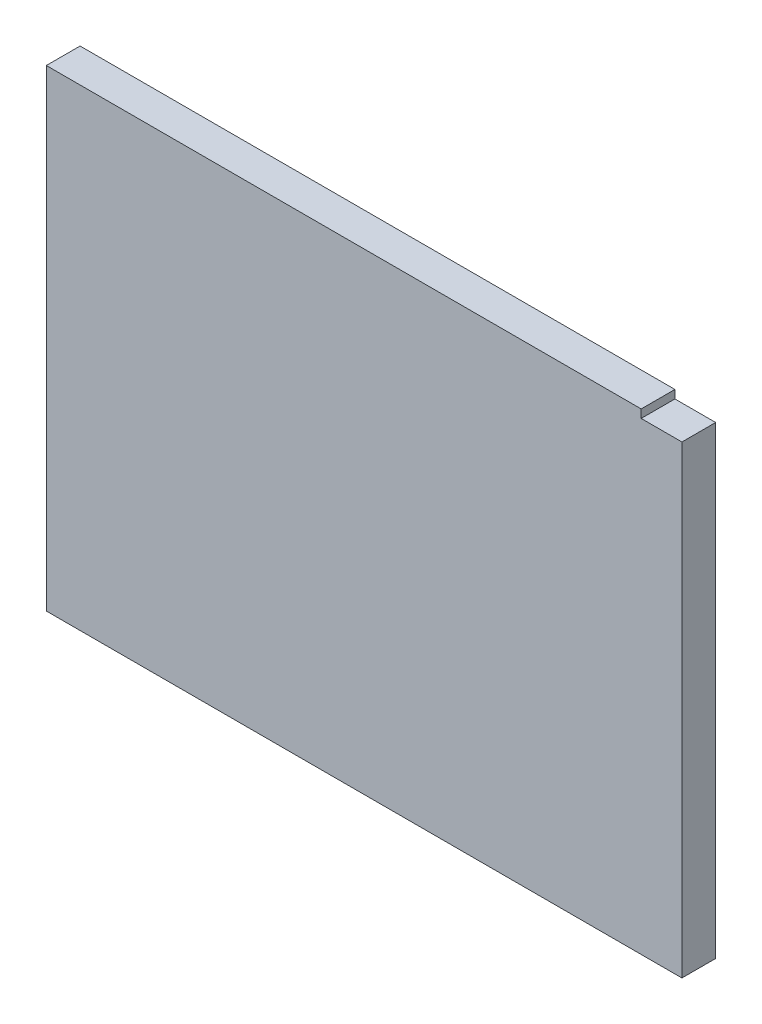
SolidWorks part; units mm, degrees
material "Pine"
ref_plane "Front Plane" through (0, 0, 0) normal (0, 0, 1) x (1, 0, 0)
ref_plane "Top Plane" through (0, 0, 0) normal (0, 1, 0) x (1, 0, 0)
ref_plane "Right Plane" through (0, 0, 0) normal (1, 0, 0) x (0, 0, -1)
sketch "Sketch1" plane through (0, 0, 0) normal (0, 0, 1) x (1, 0, 0)
  line L0 (-5300.6625, 1520.825) -> (-5451.475, 1520.825)
  line L1 (-5456.2375, 1384.3) -> (-5456.2375, 1516.0625)
  line L2 (-5557.8375, 1546.225) -> (-5194.3, 1546.225)
  line L3 (-5557.8375, 1539.875) -> (-5194.3, 1539.875)
  line L4 (-5297.4875, 1377.95) -> (-5454.65, 1377.95)
  line L5 (-5291.1375, 1384.3) -> (-5291.1375, 1516.0625)
  line L6 (-5300.6625, 1525.5875) -> (-5451.475, 1525.5875)
  line L7 (-5461, 1384.3) -> (-5461, 1516.0625)
  line L8 (-5297.4875, 1382.7125) -> (-5454.65, 1382.7125)
  line L9 (-5295.9, 1384.3) -> (-5295.9, 1516.0625)
  line L10 (-5740.4, 998.5375) -> (-5740.4, 1181.1)
  line L11 (-5740.4, 1181.1) -> (-5512.5938, 1181.1)
  line L12 (-5512.5938, 1181.1) -> (-5512.5938, 998.5375)
  line L13 (-5512.5938, 998.5375) -> (-5740.4, 998.5375)
  line L14 (-5258.5938, 1181.1) -> (-5486.4, 1181.1)
  line L15 (-5258.5938, 998.5375) -> (-5258.5938, 1181.1)
  line L16 (-5486.4, 998.5375) -> (-5258.5938, 998.5375)
  line L17 (-5486.4, 1181.1) -> (-5486.4, 998.5375)
  line L18 (-5740.4, 898.525) -> (-5011.7375, 898.525)
  line L19 (-5168.1062, 1384.3) -> (-5168.1062, 1392.2375)
  line L20 (-5176.0437, 1400.175) -> (-5245.8937, 1400.175)
  line L21 (-5253.8313, 1392.2375) -> (-5253.8313, 1384.3)
  line L22 (-5451.475, 1512.8875) -> (-5451.475, 1384.3)
  line L23 (-5303.8375, 1516.0625) -> (-5448.3, 1516.0625)
  line L24 (-5498.3062, 1384.3) -> (-5451.475, 1384.3)
  line L25 (-5253.8313, 1384.3) -> (-5300.6625, 1384.3)
  line L26 (-5584.0312, 1384.3) -> (-5740.4, 1384.3)
  line L27 (-5564.1875, 1536.7) -> (-5740.4, 1536.7)
  line L28 (-5740.4, 1357.3125) -> (-5740.4, 1206.5)
  line L29 (-5011.7375, 1357.3125) -> (-5740.4, 1357.3125)
  line L30 (-5011.7375, 1206.5) -> (-5011.7375, 1357.3125)
  line L31 (-5740.4, 1206.5) -> (-5011.7375, 1206.5)
  line L32 (-4765.675, 1549.4) -> (-4978.4, 1549.4)
  line L33 (-4765.675, 1397) -> (-4765.675, 1549.4)
  line L34 (-4978.4, 1397) -> (-4765.675, 1397)
  line L35 (-4978.4, 1549.4) -> (-4978.4, 1397)
  line L36 (-4765.675, 1371.6) -> (-4978.4, 1371.6)
  line L37 (-4765.675, 1219.2) -> (-4765.675, 1371.6)
  line L38 (-4978.4, 1219.2) -> (-4765.675, 1219.2)
  line L39 (-4978.4, 1371.6) -> (-4978.4, 1219.2)
  line L40 (-5284.7875, 803.275) -> (-5272.0875, 803.275)
  line L41 (-5187.95, 1536.7) -> (-5011.7375, 1536.7)
  line L42 (-5300.6625, 1384.3) -> (-5300.6625, 1512.8875)
  line L43 (-5740.4, 1536.7) -> (-5740.4, 1384.3)
  line L44 (-5557.8375, 1536.7) -> (-5557.8375, 1549.4)
  line L45 (-5557.8375, 1549.4) -> (-5194.3, 1549.4)
  line L46 (-5194.3, 1549.4) -> (-5194.3, 1536.7)
  line L47 (-5011.7375, 1536.7) -> (-5011.7375, 1384.3)
  line L48 (-5011.7375, 1384.3) -> (-5168.1062, 1384.3)
  line L49 (-5498.3062, 1384.3) -> (-5498.3062, 1392.2375)
  line L50 (-5506.2437, 1400.175) -> (-5576.0938, 1400.175)
  line L51 (-5584.0312, 1392.2375) -> (-5584.0312, 1384.3)
  line L52 (-5740.4, 660.4) -> (-5740.4, 898.525)
  line L53 (-5011.7375, 898.525) -> (-5011.7375, 660.4)
  line L54 (-5011.7375, 660.4) -> (-5740.4, 660.4)
  line L55 (-5291.1375, 803.275) -> (-5291.1375, 752.475)
  line L56 (-5265.7375, 752.475) -> (-5265.7375, 803.275)
  line L57 (-5284.7875, 752.475) -> (-5272.0875, 752.475)
  arc A0 (-5451.475, 1520.825) -> (-5456.2375, 1516.0625) centre (-5451.475, 1516.0625) ccw
  arc A1 (-5461, 1384.3) -> (-5454.65, 1377.95) centre (-5454.65, 1384.3) ccw
  arc A2 (-5297.4875, 1377.95) -> (-5291.1375, 1384.3) centre (-5297.4875, 1384.3) ccw
  circle A3 centre (-5037.9312, 1233.4875) radius 1.5875
  circle A4 centre (-5037.9312, 1328.7375) radius 1.5875
  circle A5 centre (-5714.2063, 1233.4875) radius 1.5875
  circle A6 centre (-5714.2063, 1328.7375) radius 1.5875
  circle A7 centre (-5018.0875, 1333.5) radius 1.5875
  circle A8 centre (-5018.0875, 1231.9) radius 1.5875
  circle A9 centre (-5734.05, 1231.9) radius 1.5875
  circle A10 centre (-5734.05, 1333.5) radius 1.5875
  circle A11 centre (-5734.05, 1511.3) radius 1.5875
  circle A12 centre (-5734.05, 1409.7) radius 1.5875
  circle A13 centre (-5018.0875, 1511.3) radius 1.5875
  circle A14 centre (-5018.0875, 1409.7) radius 1.5875
  arc A15 (-5557.8375, 1546.225) -> (-5557.8375, 1539.875) centre (-5557.8375, 1543.05) ccw
  arc A16 (-5194.3, 1539.875) -> (-5194.3, 1546.225) centre (-5194.3, 1543.05) ccw
  arc A17 (-5291.1375, 1516.0625) -> (-5300.6625, 1525.5875) centre (-5300.6625, 1516.0625) ccw
  arc A18 (-5451.475, 1525.5875) -> (-5461, 1516.0625) centre (-5451.475, 1516.0625) ccw
  arc A19 (-5456.2375, 1384.3) -> (-5454.65, 1382.7125) centre (-5454.65, 1384.3) ccw
  arc A20 (-5297.4875, 1382.7125) -> (-5295.9, 1384.3) centre (-5297.4875, 1384.3) ccw
  arc A21 (-5295.9, 1516.0625) -> (-5300.6625, 1520.825) centre (-5300.6625, 1516.0625) ccw
  circle A22 centre (-5702.3, 892.175) radius 1.5875
  circle A23 centre (-5734.05, 860.425) radius 1.5875
  circle A24 centre (-5474.8906, 892.175) radius 1.5875
  circle A25 centre (-5277.2469, 892.175) radius 1.5875
  circle A26 centre (-5049.8375, 892.175) radius 1.5875
  circle A27 centre (-5018.0875, 860.425) radius 1.5875
  circle A28 centre (-5296.6938, 1174.75) radius 1.5875
  circle A29 centre (-5448.3, 1174.75) radius 1.5875
  circle A30 centre (-5264.9437, 1155.7) radius 1.5875
  circle A31 centre (-5264.9437, 1023.9375) radius 1.5875
  circle A32 centre (-5518.9438, 1155.7) radius 1.5875
  circle A33 centre (-5518.9438, 1023.9375) radius 1.5875
  circle A34 centre (-5702.3, 1004.8875) radius 1.5875
  circle A35 centre (-5550.6937, 1004.8875) radius 1.5875
  arc A36 (-5576.0938, 1400.175) -> (-5584.0312, 1392.2375) centre (-5576.0938, 1392.2375) ccw
  arc A37 (-5168.1062, 1392.2375) -> (-5176.0437, 1400.175) centre (-5176.0437, 1392.2375) ccw
  arc A38 (-5245.8937, 1400.175) -> (-5253.8313, 1392.2375) centre (-5245.8937, 1392.2375) ccw
  arc A39 (-5448.3, 1516.0625) -> (-5451.475, 1512.8875) centre (-5448.3, 1512.8875) ccw
  arc A40 (-5284.7875, 803.275) -> (-5291.1375, 803.275) centre (-5287.9625, 803.275) ccw
  circle A41 centre (-5679.2812, 1026.3187) radius 1.5875
  circle A42 centre (-5679.2812, 1153.3187) radius 1.5875
  circle A43 centre (-5571.3313, 1153.3187) radius 1.5875
  circle A44 centre (-5571.3313, 1026.3187) radius 1.5875
  circle A45 centre (-5317.3312, 1153.3187) radius 1.5875
  circle A46 centre (-5317.3312, 1026.3187) radius 1.5875
  circle A47 centre (-5425.2812, 1026.3187) radius 1.5875
  circle A48 centre (-5425.2812, 1153.3187) radius 1.5875
  arc A49 (-5194.3, 1536.7) -> (-5187.95, 1536.7) centre (-5191.125, 1536.7) ccw
  arc A50 (-5564.1875, 1536.7) -> (-5557.8375, 1536.7) centre (-5561.0125, 1536.7) ccw
  arc A51 (-5300.6625, 1512.8875) -> (-5303.8375, 1516.0625) centre (-5303.8375, 1512.8875) ccw
  arc A52 (-5498.3062, 1392.2375) -> (-5506.2437, 1400.175) centre (-5506.2437, 1392.2375) ccw
  circle A53 centre (-5712.46, 784.225) radius 4.7625
  arc A54 (-5272.0875, 752.475) -> (-5265.7375, 752.475) centre (-5268.9125, 752.475) ccw
  arc A55 (-5291.1375, 752.475) -> (-5284.7875, 752.475) centre (-5287.9625, 752.475) ccw
  circle A56 centre (-5182.3938, 684.2125) radius 3.175
  circle A57 centre (-5239.5437, 684.2125) radius 3.175
  circle A58 centre (-5512.5938, 684.2125) radius 3.175
  circle A59 centre (-5569.7437, 684.2125) radius 3.175
  circle A60 centre (-5474.8906, 666.75) radius 1.5875
  circle A61 centre (-5277.2469, 666.75) radius 1.5875
  circle A62 centre (-5734.05, 698.5) radius 1.5875
  circle A63 centre (-5702.3, 666.75) radius 1.5875
  circle A64 centre (-5049.8375, 666.75) radius 1.5875
  circle A65 centre (-5018.0875, 698.5) radius 1.5875
  circle A66 centre (-5713.73, 835.025) radius 4.7625
  circle A67 centre (-5712.46, 819.785) radius 4.7625
  circle A68 centre (-5712.46, 802.005) radius 4.7625
  circle A69 centre (-5714.2063, 1314.45) radius 3.175
  circle A70 centre (-5037.9312, 1314.45) radius 3.175
  arc A71 (-5265.7375, 803.275) -> (-5272.0875, 803.275) centre (-5268.9125, 803.275) ccw
  ellipse E0 centre (-5371.3062, 1089.8188) end of major axis (-5277.6438, 1089.8188) minor radius 65.0875
  ellipse E1 centre (-5625.3062, 1089.8188) end of major axis (-5531.6438, 1089.8188) minor radius 65.0875
sketch "SideOutline" plane through (0, 0, 0) normal (0, 0, 1) x (1, 0, 0)
  line L0 (-4763.135, 1379.22) -> (-4763.135, 1219.2)
  line L1 (-4763.135, 1219.2) -> (-4978.4, 1219.2)
  line L2 (-4978.4, 1219.2) -> (-4978.4, 1379.22)
  line L3 (-4978.4, 1379.22) -> (-4763.135, 1379.22)
  line L4 (-4870.7675, 1379.22) -> (-4870.7675, 1219.2) construction
  line L5 (-4870.7675, 1299.21) -> (-4978.4, 1299.21) construction
  line L6 (-4870.7675, 1299.21) -> (-4763.135, 1299.21) construction
extrude "SideOutline_Thickness" add sketch "SideOutline" against normal blind 11.43
sketch "Sketch2" plane through (0, 0, -11.43) normal (0, 0, -1) x (-1, 0, 0)
  line L0 (4776.9335, 1376.426) -> (4776.9335, 1379.22)
  line L1 (4763.135, 1379.22) -> (4978.4, 1379.22) construction
  line L2 (4776.9335, 1379.22) -> (4763.135, 1379.22)
  line L3 (4763.135, 1379.22) -> (4763.135, 1376.426)
  line L4 (4763.135, 1219.2) -> (4763.135, 1379.22) construction
  line L5 (4776.9335, 1376.426) -> (4745.59, 1376.426) construction
  line L6 (4763.135, 1376.426) -> (4776.9335, 1376.426)
extrude "Cut-Extrude1" cut sketch "Sketch2" against normal up to surface (11.43 mm away) up to face at (-4870.7675, 1299.21, 0)
